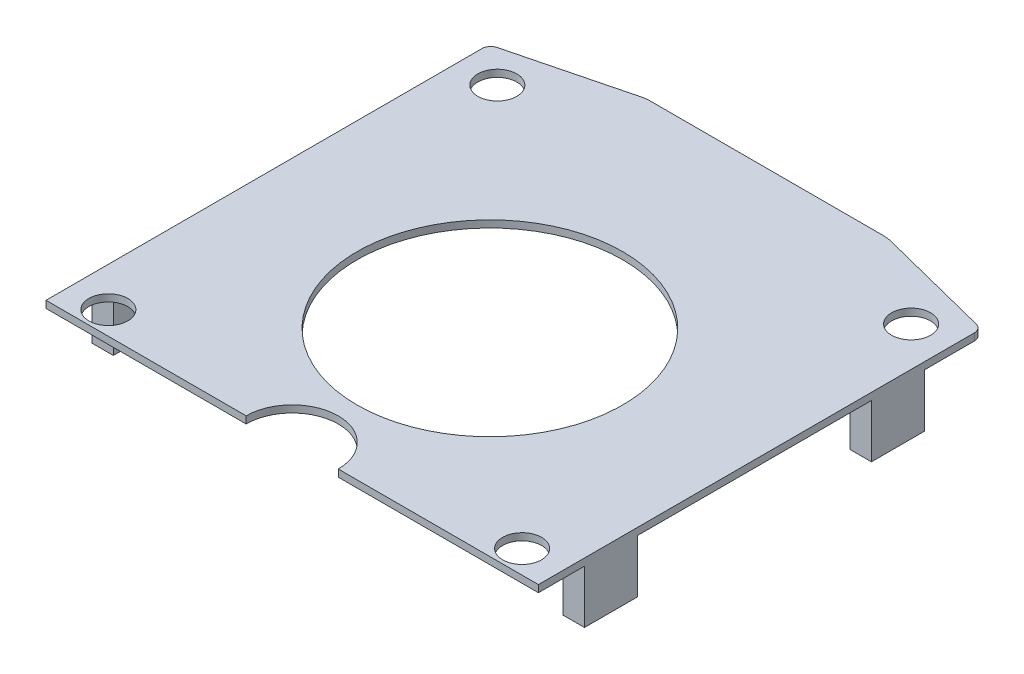
SolidWorks part; units mm, degrees
material "Polybutadiene (PB)"
ref_plane "Front Plane" through (0, 0, 0) normal (0, 0, 1) x (1, 0, 0)
ref_plane "Top Plane" through (0, 0, 0) normal (0, 1, 0) x (1, 0, 0)
ref_plane "Right Plane" through (0, 0, 0) normal (1, 0, 0) x (0, 0, -1)
sketch "Sketch1" plane through (0, 0, 0) normal (0, 1, 0) x (1, 0, 0)
  line L0 (0, 11.9) -> (0, 13.8341) construction
  line L1 (-3.6651, 0) -> (-10.2349, 0)
  line L2 (0, 1.0944) -> (0, 24.2056)
  line L3 (-3.6651, 25.3) -> (-10.2349, 25.3)
  line L4 (-13.9, 1.0944) -> (-13.9, 24.2056)
  line L5 (-3.54, 25.3) -> (-3.54, 27.2341) construction
  line L6 (-13.9, 24.2056) -> (-13.9, 27.2341) construction
  line L7 (-10.36, 25.3) -> (-10.36, 27.2341) construction
  line L8 (-13.9, 24.4) -> (14.5836, 24.4) construction
  line L9 (-13.7116, 24.4479) -> (-10.4813, 25.2692)
  line L10 (-3.4187, 25.2692) -> (-0.1884, 24.4479)
  line L11 (-10.36, 27.2341) -> (-3.54, 27.2341) construction
  line L12 (-6.95, 27.2341) -> (-6.95, 25.3) construction
  line L13 (-0.1884, 24.4479) -> (-3.4187, 25.2692)
  line L14 (-10.2349, 0) -> (-6.95, 0) construction
  line L15 (-6.95, 0) -> (-6.95, 25.3) construction
  line L16 (-6.95, 12.65) -> (0, 12.65) construction
  line L17 (-3.4187, 0.0308) -> (-0.1884, 0.8521)
  line L18 (-3.6651, 0) -> (-10.2349, 0)
  line L19 (-13.7116, 0.8521) -> (-10.4813, 0.0308)
  line L20 (0, 1.0944) -> (0, -13.6503) construction
  line L21 (-3.6651, 0) -> (0, 0) construction
  line L22 (0, 12.65) -> (-13.9, 12.65)
  line L23 (0, 11.9) -> (-13.9, 11.9)
  arc A0 (-10.2349, 25.3) -> (-10.4813, 25.2692) centre (-10.2349, 24.3) ccw
  arc A1 (-13.7116, 24.4479) -> (-13.9, 24.2056) centre (-13.65, 24.2056) ccw
  arc A2 (-3.6651, 25.3) -> (-3.4187, 25.2692) centre (-3.6651, 24.3) cw
  arc A3 (-0.1884, 24.4479) -> (0, 24.2056) centre (-0.25, 24.2056) cw
  arc A4 (-0.1884, 0.8521) -> (0, 1.0944) centre (-0.25, 1.0944) ccw
  arc A5 (-3.6651, 0) -> (-3.4187, 0.0308) centre (-3.6651, 1) ccw
  arc A6 (-10.2349, 0) -> (-10.4813, 0.0308) centre (-10.2349, 1) cw
  arc A7 (-13.7116, 0.8521) -> (-13.9, 1.0944) centre (-13.65, 1.0944) cw
  dimension "D3" = 1
  dimension "D4" = 0.25
  dimension "D1" = 3.54
  dimension "D2" = 0.9
  dimension "D5" = 25.3
  dimension "D6" = 24.2056
  dimension "D7" = 24.4479
  dimension "D8" = 1.9341
  dimension "D9" = 13.9
  dimension "D10" = 0.75
extrude "Boss-Extrude1" add sketch "Sketch1" along normal blind 0.2 contours A3 L10 A2 L3 A0 L9 A1 L4 L22 L2 | L23 L2 L22 L4
sketch "Sketch2" plane through (0, 0.2, 0) normal (0, 1, 0) x (1, 0, 0)
  line L0 (-3.6651, 25.3) -> (-10.2349, 25.3) construction
  line L1 (0, 11.9) -> (0, 24.2056) construction
  line L2 (-6.95, 11.9) -> (-6.95, 25.3) construction
  line L3 (0, 11.9) -> (-13.9, 11.9) construction
  circle A0 centre (-1.11, 23.53) radius 0.55
  circle A1 centre (-1.11, 12.55) radius 0.55
  circle A2 centre (-12.79, 23.53) radius 0.55
  circle A3 centre (-12.79, 12.55) radius 0.55
  circle A4 centre (-6.95, 17.48) radius 3.75
  dimension "D1" = 1.77
  dimension "D2" = 1.11
  dimension "D3" = 1.1
  dimension "D4" = 12.75
  dimension "D6" = 7.5
  dimension "D5" = 7.82
extrude "Cut-Extrude1" cut sketch "Sketch2" against normal blind 0.3
sketch "Sketch3" plane through (0, 0.2, 0) normal (0, 1, 0) x (1, 0, 0)
sketch "Sketch4" plane through (0, 0.2, 0) normal (0, 1, 0) x (1, 0, 0)
  line L0 (0, 11.9) -> (-13.9, 11.9) construction
  line L1 (-5.65, 11.9) -> (-8.25, 11.9)
  arc A0 (-5.65, 11.9) -> (-8.25, 11.9) centre (-6.95, 11.9) ccw
  dimension "D1" = 1.3
extrude "Cut-Extrude2" cut sketch "Sketch4" against normal blind 0.3
sketch "Sketch5" plane through (0, 0.2, 0) normal (0, 1, 0) x (1, 0, 0)
  line L0 (-3.6651, 25.3) -> (0.6859, 25.3) construction
  line L1 (0, 24.2056) -> (0, 25.3) construction
sketch "Sketch6" plane through (0, 0, 0) normal (1, 0, 0) x (0, 0, -1)
  line L0 (22.8, 0) -> (22.8, -1.5168) construction
  line L1 (11.9, 0) -> (24.2056, 0) construction
  line L2 (25.3, 0.2) -> (25.3, -1.6204) construction
  line L3 (24.2056, 0.2) -> (25.3, 0.2) construction
  line L4 (22.8, 0) -> (22.8, -1.5)
  line L5 (22.8, -1.5) -> (21.3, -1.5)
  line L6 (21.3, -1.5) -> (21.3, 0)
  line L7 (21.3, 0) -> (22.8, 0)
  line L8 (14.7, 0) -> (14.7, -1.5)
  line L9 (14.7, -1.5) -> (13.2, -1.5)
  line L10 (13.2, -1.5) -> (13.2, 0)
  line L11 (14.7, 0) -> (13.2, 0)
  dimension "D1" = 2.5
  dimension "D2" = 1.5
  dimension "D3" = 1.5
  dimension "D4" = 6.6
extrude "Boss-Extrude2" add sketch "Sketch6" against normal blind 0.6
sketch "Sketch7" plane through (0, 0, 0) normal (0, -1, 0) x (1, 0, 0)
  line L0 (-6.95, -25.3) -> (-6.95, -11.9) construction
  line L1 (-3.6651, -25.3) -> (-10.2349, -25.3) construction
  line L2 (0, -22.8) -> (0, -21.3)
  line L3 (0, -21.3) -> (-0.6, -21.3)
  line L4 (-0.6, -21.3) -> (-0.6, -22.8)
  line L5 (-0.6, -22.8) -> (0, -22.8)
  line L6 (0, -14.7) -> (-0.6, -14.7)
  line L7 (-0.6, -14.7) -> (-0.6, -13.2)
  line L8 (-0.6, -13.2) -> (0, -13.2)
  line L9 (0, -13.2) -> (0, -14.7)
  line L10 (-13.3, -13.2) -> (-13.9, -13.2)
  line L11 (-13.3, -14.7) -> (-13.3, -13.2)
  line L12 (-13.9, -14.7) -> (-13.3, -14.7)
  line L13 (-13.9, -13.2) -> (-13.9, -14.7)
  line L14 (-13.3, -22.8) -> (-13.9, -22.8)
  line L15 (-13.9, -22.8) -> (-13.9, -21.3)
  line L16 (-13.9, -21.3) -> (-13.3, -21.3)
  line L17 (-13.3, -21.3) -> (-13.3, -22.8)
extrude "Boss-Extrude3" add sketch "Sketch7" along normal blind 1.5
